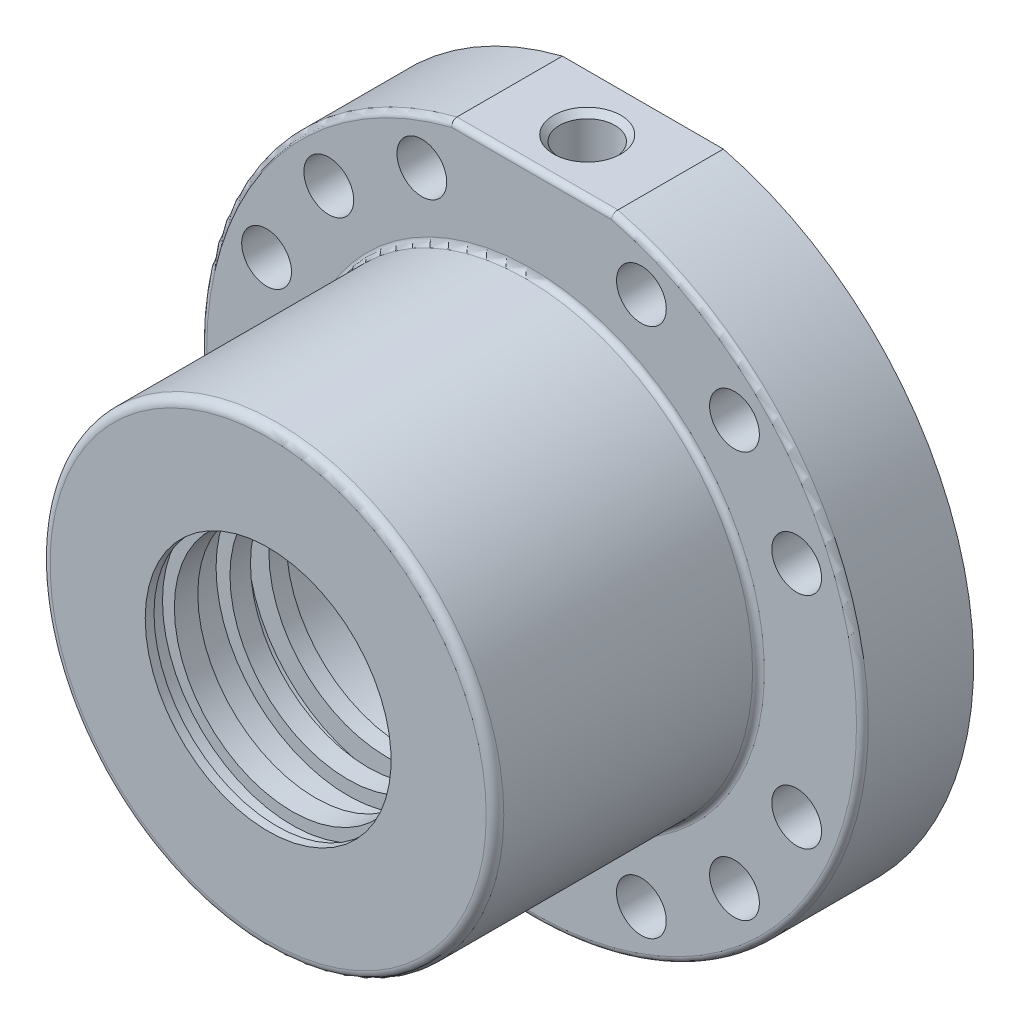
SolidWorks part; units mm, degrees
ref_plane "Front Plane" through (0, 0, 0) normal (0, 0, 1) x (1, 0, 0)
ref_plane "Top Plane" through (0, 0, 0) normal (0, 1, 0) x (1, 0, 0)
ref_plane "Right Plane" through (0, 0, 0) normal (1, 0, 0) x (0, 0, -1)
sketch "Sketch1" plane through (0, 0, 0) normal (0, 0, 1) x (1, 0, 0)
  circle A0 centre (0, 0) radius 113
  dimension "D1" = 226
extrude "Boss-Extrude1" add sketch "Sketch1" along normal mid plane 148
sketch "Sketch2" plane through (0, 0, -74) normal (0, 0, -1) x (-1, 0, 0)
  circle A0 centre (0, 0) radius 70
  circle A1 centre (0, 0) radius 129
  dimension "D1" = 140
extrude "Cut-Extrude1" cut sketch "Sketch2" against normal blind 20
sketch "Sketch3" plane through (0, 0, 0) normal (1, 0, 0) x (0, 0, -1)
  line L0 (0, 0) -> (-152.7563, 0) construction
  line L1 (-74, 154.6191) -> (16, 154.6191)
  line L2 (-74, 154.6191) -> (-74, 77.5)
  line L3 (-74, 77.5) -> (16, 77.5)
  line L4 (16, 154.6191) -> (16, 77.5)
  line L5 (-74, 113) -> (-74, -113) construction
  dimension "D1" = 90
  dimension "D2" = 155
revolve "Cut-Revolve1" cut sketch "Sketch3" angle 360 about L0
sketch "Sketch6" plane through (0, 0, 0) normal (1, 0, 0) x (0, 0, -1)
  line L0 (0, 0) -> (116.2083, 0) construction
  line L1 (74, -70) -> (74, 70) construction
  line L2 (63, 77.1564) -> (69, 77.1564)
  line L3 (63, 77.1564) -> (63, 66)
  line L4 (63, 66) -> (69, 66)
  line L5 (69, 77.1564) -> (69, 66)
  dimension "D1" = 132
  dimension "D2" = 6
  dimension "D3" = 5
revolve "Cut-Revolve2" cut sketch "Sketch6" angle 360 about L0
chamfer "Chamfer1" distance 1 angle 45 1 edges at (-70, 0, -74)
sketch "Sketch9" plane through (0, 0, 0) normal (0, 0, 1) x (1, 0, 0)
  line L0 (0, 0) -> (0, 113) construction
  line L1 (-27.5, 153.9069) -> (27.5, 153.9069)
  line L2 (-27.5, 153.9069) -> (-27.5, 109.6027)
  line L3 (-27.5, 109.6027) -> (27.5, 109.6027)
  line L4 (27.5, 153.9069) -> (27.5, 109.6027)
  circle A0 centre (0, 0) radius 113 construction
  dimension "D1" = 55
  dimension "D2" = 55
extrude "Cut-Extrude2" cut sketch "Sketch9" against normal mid plane 245
hole_wizard "1/2-14 NPSM Tapped Hole1" positions "Sketch10" profile "Sketch11" tap size "1/2-14 NPSM" standard "ANSI Inch"
sketch "Sketch10" plane through (0, 109.6027, 0) normal (0, 1, 0) x (1, 0, 0)
  line L0 (0, 54) -> (0, 16) construction
  line L1 (27.5, 54) -> (-27.5, 54) construction
  line L2 (-77.5, 16) -> (77.5, 16) construction
  point P0 (0, 35)
cosmetic thread "Hole Thread1" parameters "D1"=41.8084, "D2"=20.9042
sketch "Sketch11" plane through (0, 109.6027, -35) normal (1, 0, 0) x (0, 0, 1)
  line L0 (0, 0) -> (0, 105.7003)
  line L1 (0, 105.7003) -> (9.4869, 100)
  line L2 (9.4869, 100) -> (9.4869, 0)
  line L5 (9.4869, 0) -> (0, 0)
  line L10 (0, 105.7003) -> (-9.4869, 100) construction
  line L11 (0, -6.35) -> (0, 107.95) construction
  dimension "Tap Drill Dia." = 18.9738
  dimension "Tap Drill Depth" = 100
  dimension "Drill Angle" = 118
sketch "Sketch7" plane through (0, 0, 0) normal (1, 0, 0) x (0, -1, 0)
  line L0 (0, 0) -> (0, -108.8382) construction
  line L1 (-42, -74) -> (-42, -71)
  line L2 (-77.5, -74) -> (77.5, -74) construction
  line L3 (-42, -71) -> (-44.3, -71)
  line L4 (-44.3, -71) -> (-44.3, -65.8)
  line L5 (-44.3, -65.8) -> (-40.25, -65.8)
  line L6 (-40.25, -65.8) -> (-40.25, -57.8)
  line L7 (-40.25, -57.8) -> (-45, -57.8)
  line L8 (-45, -57.8) -> (-45, -46.8)
  line L9 (-45, -46.8) -> (-40.25, -46.8)
  line L10 (-40.25, -46.8) -> (-40.25, -39.8)
  line L11 (-40.25, -39.8) -> (-47.55, -39.8)
  line L12 (-47.55, -39.8) -> (-47.55, -33.5)
  line L13 (-47.55, -33.5) -> (-40.25, -33.5)
  line L14 (-40.25, -33.5) -> (-40.25, -27.5)
  line L15 (-40.25, -27.5) -> (-42.5, -27.5)
  line L16 (-42.5, -27.5) -> (-42.5, 22.5)
  line L17 (-36.1501, 96.1077) -> (0, 96.1077)
  line L18 (0, 96.1077) -> (0, -74)
  line L19 (0, -74) -> (-42, -74)
  line L20 (-42.5, 22.5) -> (-45, 22.5)
  line L21 (-45, 22.5) -> (-45, 96.1077)
  line L22 (-45, 96.1077) -> (-36.1501, 96.1077)
  dimension "D1" = 88.6
  dimension "D2" = 84
  dimension "D3" = 5.2
  dimension "D4" = 90
  dimension "D5" = 11
  dimension "D6" = 95.1
  dimension "D7" = 6.3
  dimension "D8" = 3
  dimension "D9" = 8
  dimension "D10" = 7
  dimension "D11" = 6
  dimension "D12" = 85
  dimension "D13" = 80.5
  dimension "D14" = 90
  dimension "D15" = 50
revolve "Cut-Revolve3" cut sketch "Sketch7" angle 360 about L0
chamfer "Chamfer2" distance 2 angle 45 1 edges at (0, 109.6027, -25.5131)
sketch "Sketch13" plane through (0, 0, -16) normal (0, 0, 1) x (1, 0, 0)
  line L0 (0, 0) -> (0, 98) construction
  line L1 (0, 0) -> (-37.503, 90.5402) construction
  line L2 (0, 0) -> (-69.2965, 69.2965) construction
  line L3 (0, 0) -> (-90.5402, 37.503) construction
  circle A0 centre (0, 0) radius 98 construction
  circle A1 centre (-69.2965, 69.2965) radius 8.5
  circle A2 centre (-37.503, 90.5402) radius 8.5
  circle A3 centre (-90.5402, 37.503) radius 8.5
  dimension "D1" = 196
  dimension "D2" = 17
  dimension "D3" = 17
  dimension "D4" = 17
  dimension "D5" = 22.5
  dimension "D6" = 22.5
  dimension "D7" = 22.5
extrude "Cut-Extrude3" cut sketch "Sketch13" against normal through all
pattern_circular "CirPattern3" count 4 over 360 about axis through (0, 0, 0) along (0, 0, 1) of "Cut-Extrude3"
fillet "Fillet1" radius 2 3 edges at (-77.5, 0, -16) (0, 109.6027, -16) (0, -113, -16)
fillet "Fillet2" radius 3 1 edges at (-77.5, 0, 74)
